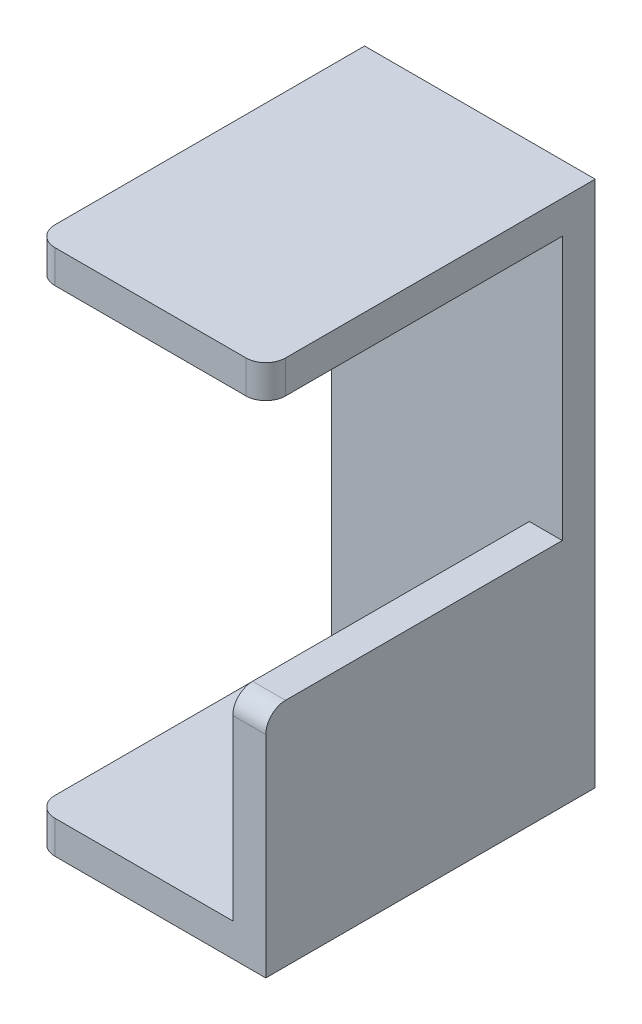
SolidWorks part; units mm, degrees
ref_plane "前基準面" through (0, 0, 0) normal (0, 0, 1) x (1, 0, 0)
ref_plane "上基準面" through (0, 0, 0) normal (0, 1, 0) x (1, 0, 0)
ref_plane "右基準面" through (0, 0, 0) normal (1, 0, 0) x (0, 0, -1)
sketch "草圖1" plane through (0, 0, 0) normal (0, 0, 1) x (1, 0, 0)
  line L1 (-47.1382, 34.8052) -> (-12.1382, 34.8052)
  line L2 (-47.1382, 34.8052) -> (-47.1382, -45.1948)
  line L3 (-47.1382, -45.1948) -> (-12.1382, -45.1948)
  line L4 (-12.1382, 34.8052) -> (-12.1382, -45.1948)
  dimension "D1" = 80
  dimension "D2" = 35
extrude "填料-伸長1" add sketch "草圖1" along normal blind 5
sketch "草圖2" plane through (0, 0, 5) normal (0, 0, 1) x (1, 0, 0)
  line L0 (-12.1382, -45.1948) -> (-12.1382, 34.8052) construction
  line L1 (-47.1382, 34.8052) -> (-12.1382, 34.8052)
  line L2 (-47.1382, 34.8052) -> (-47.1382, 29.8052)
  line L3 (-47.1382, 29.8052) -> (-12.1382, 29.8052)
  line L4 (-12.1382, 34.8052) -> (-12.1382, 29.8052)
  line L6 (-47.1382, -45.1948) -> (-12.1382, -45.1948)
  line L7 (-47.1382, -45.1948) -> (-47.1382, -40.1948)
  line L8 (-47.1382, -40.1948) -> (-12.1382, -40.1948)
  line L9 (-12.1382, -45.1948) -> (-12.1382, -40.1948)
  line L10 (-12.1382, -45.1948) -> (-17.1382, -45.1948)
  line L11 (-12.1382, -45.1948) -> (-12.1382, -10.1948)
  line L12 (-12.1382, -10.1948) -> (-17.1382, -10.1948)
  line L13 (-17.1382, -45.1948) -> (-17.1382, -10.1948)
  dimension "D1" = 5
  dimension "D2" = 5
  dimension "D3" = 5
  dimension "D4" = 35
extrude "填料-伸長2" add sketch "草圖2" along normal blind 45 contours L2 L1 L4 L3 | L11 L10 L13 L12 | L7 L6 L9 L8
fillet "圓角2" radius 3 4 edges at (-47.1382, -42.6948, 50) (-14.6382, -10.1948, 50) (-47.1382, 32.3052, 50) (-12.1382, 32.3052, 50)
